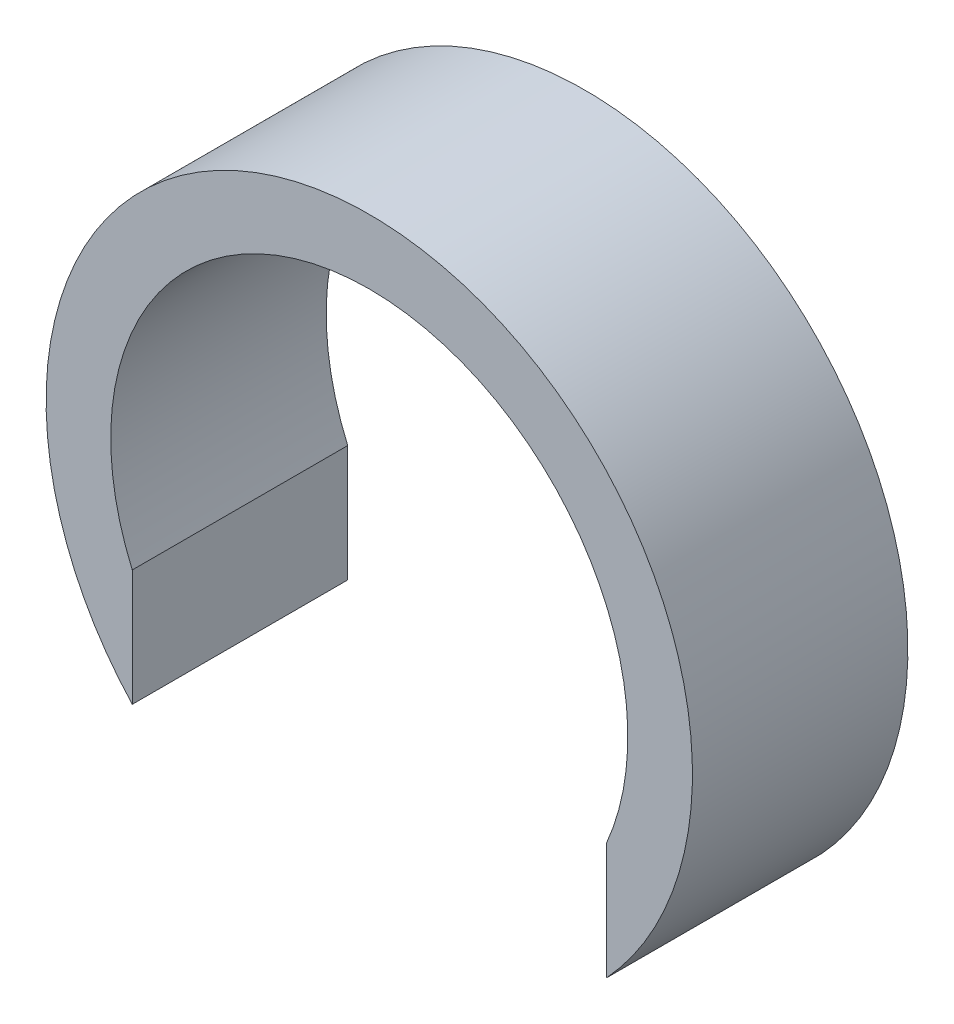
SolidWorks part; units mm, degrees
ref_plane "正面" through (0, 0, 0) normal (0, 0, 1) x (1, 0, 0)
ref_plane "平面" through (0, 0, 0) normal (0, 1, 0) x (1, 0, 0)
ref_plane "右側面" through (0, 0, 0) normal (1, 0, 0) x (0, 0, -1)
sketch "ｽｹｯﾁ1" plane through (0, 0, 0) normal (0, 0, 1) x (1, 0, 0)
  line L3 (5.5, -5.099) -> (5.5, -2.3979)
  line L5 (-1.5, -10.7982) -> (1.5, -4.2018) construction
  line L6 (-1.5, -4.2018) -> (1.5, -10.7982) construction
  line L8 (-5.5, -5.099) -> (-5.5, -2.3979)
  line L9 (5.5, -19.9963) -> (-5.5, 0) construction
  line L10 (5.5, 0) -> (-5.5, -19.9963) construction
  arc A0 (5.5, -2.3979) -> (-5.5, -2.3979) centre (0, 0) ccw
  arc A1 (5.5, -5.099) -> (-5.5, -5.099) centre (0, 0) ccw
  point P1 (0, -9.9982)
  point P4 (0, -7.5)
  dimension "D1" = 12
  dimension "D2" = 15
  dimension "D3" = 3
  dimension "D4" = 11
extrude "ﾎﾞｽ - 押し出し1" add sketch "ｽｹｯﾁ1" along normal blind 5
